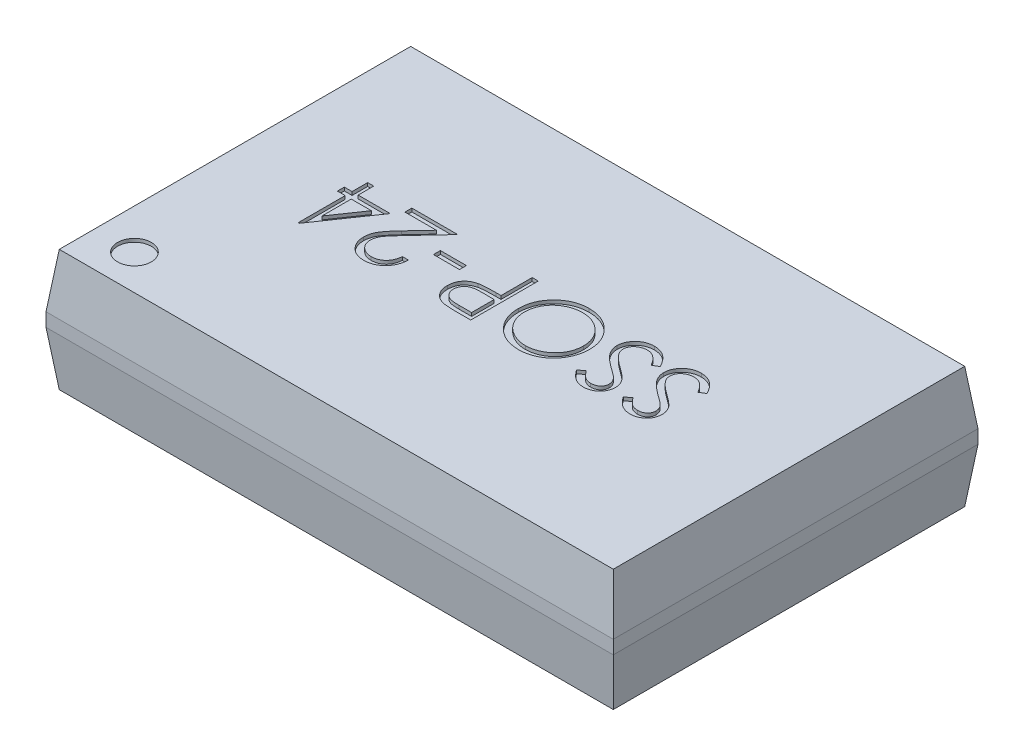
SolidWorks part; units mm, degrees
ref_plane "Front Plane" through (0, 0, 0) normal (0, 0, 1) x (1, 0, 0)
ref_plane "Top Plane" through (0, 0, 0) normal (0, 1, 0) x (1, 0, 0)
ref_plane "Right Plane" through (0, 0, 0) normal (1, 0, 0) x (0, 0, -1)
sketch "Sketch1" plane through (0, 0, 0) normal (0, 1, 0) x (1, 0, 0)
  line L1 (0, 0) -> (8.4, 0)
  line L2 (0, 0) -> (0, 5.4)
  line L3 (0, 5.4) -> (8.4, 5.4)
  line L4 (8.4, 0) -> (8.4, 5.4)
extrude "Extrude1" add sketch "Sketch1" along normal blind 1.8
chamfer "Chamfer1" distance 0.8 angle 7 4 edges at (0, 1.8, -2.7) (4.2, 1.8, -5.4) (8.4, 1.8, -2.7) (4.2, 1.8, 0)
chamfer "Chamfer2" distance 0.8 angle 7 4 edges at (8.4, 0, -2.7) (4.2, 0, -5.4) (0, 0, -2.7) (4.2, 0, 0)
sketch "Sketch3" plane through (0, 1.8, 0) normal (0, 1, 0) x (-1, 0, 0)
  circle A0 centre (-0.6909, -0.6186) radius 0.25
extrude "Cut-Extrude1" cut sketch "Sketch3" against normal blind 0.05
sketch "Sketch4" plane through (0, 1.8, 0) normal (0, 1, 0) x (-1, 0, 0)
  text T0 "SSOP-24" font "Century Gothic" height 1
extrude "Cut-Extrude2" cut sketch "Sketch4" against normal blind 0.05
